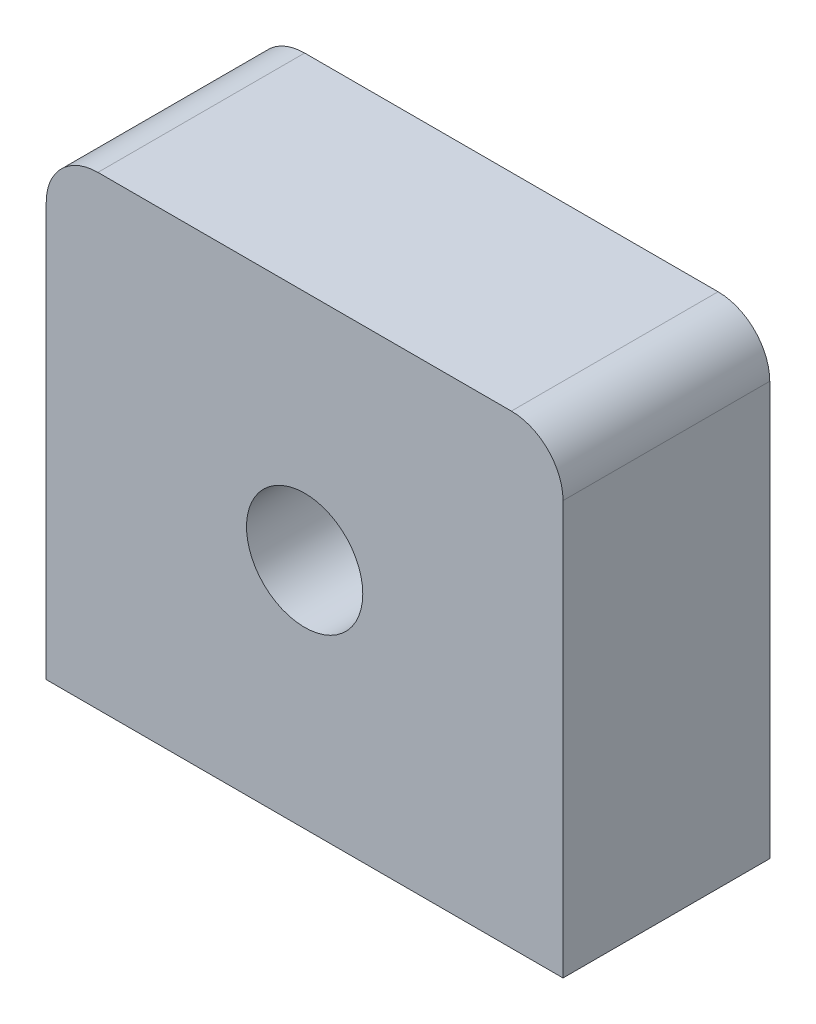
SolidWorks part; units mm, degrees
ref_plane "Спереди" through (0, 0, 0) normal (0, 0, 1) x (1, 0, 0)
ref_plane "Сверху" through (0, 0, 0) normal (0, 1, 0) x (1, 0, 0)
ref_plane "Справа" through (0, 0, 0) normal (1, 0, 0) x (0, 0, -1)
sketch "Эскиз1" plane through (0, 0, 0) normal (0, 0, 1) x (1, 0, 0)
  line L0 (0, 0) -> (0, 16)
  line L1 (2, 18) -> (18, 18)
  line L2 (20, 16) -> (20, 0)
  line L3 (20, 0) -> (0, 0)
  circle A0 centre (10, 9) radius 2.25
  arc A1 (0, 16) -> (2, 18) centre (2, 16) cw
  arc A2 (20, 16) -> (18, 18) centre (18, 16) ccw
  dimension "D1" = 2
extrude "Бобышка-Вытянуть1" add sketch "Эскиз1" along normal blind 8
